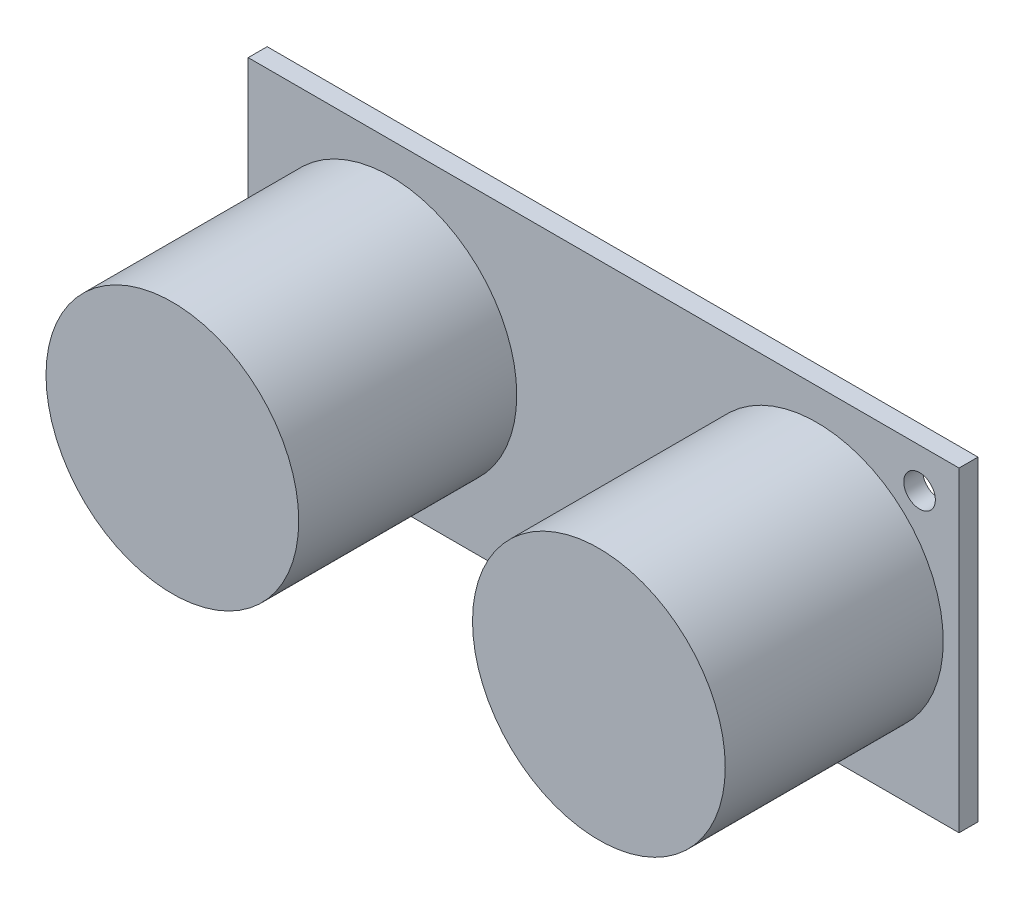
SolidWorks part; units mm, degrees
ref_plane "Front Plane" through (0, 0, 0) normal (0, 0, 1) x (1, 0, 0)
ref_plane "Top Plane" through (0, 0, 0) normal (0, 1, 0) x (1, 0, 0)
ref_plane "Right Plane" through (0, 0, 0) normal (1, 0, 0) x (0, 0, -1)
sketch "Sketch1" plane through (0, 0, 0) normal (0, 0, 1) x (1, 0, 0)
  line L1 (-22.5, 10) -> (22.5, 10)
  line L2 (-22.5, 10) -> (-22.5, -10)
  line L3 (-22.5, -10) -> (22.5, -10)
  line L4 (22.5, 10) -> (22.5, -10)
  circle A0 centre (20, 7.5) radius 1
  circle A1 centre (-20, -7.5) radius 1
  point P10 (0, 0)
  dimension "D1" = 2
extrude "Boss-Extrude1" add sketch "Sketch1" along normal blind 1.2
sketch "Sketch2" plane through (0, 0, 1.2) normal (0, 0, 1) x (1, 0, 0)
  circle A0 centre (13.5, 0) radius 8
  circle A1 centre (-13.5, 0) radius 8
  point P6 (0, 0)
  dimension "D1" = 2
extrude "Boss-Extrude2" add sketch "Sketch2" along normal blind 13.8
